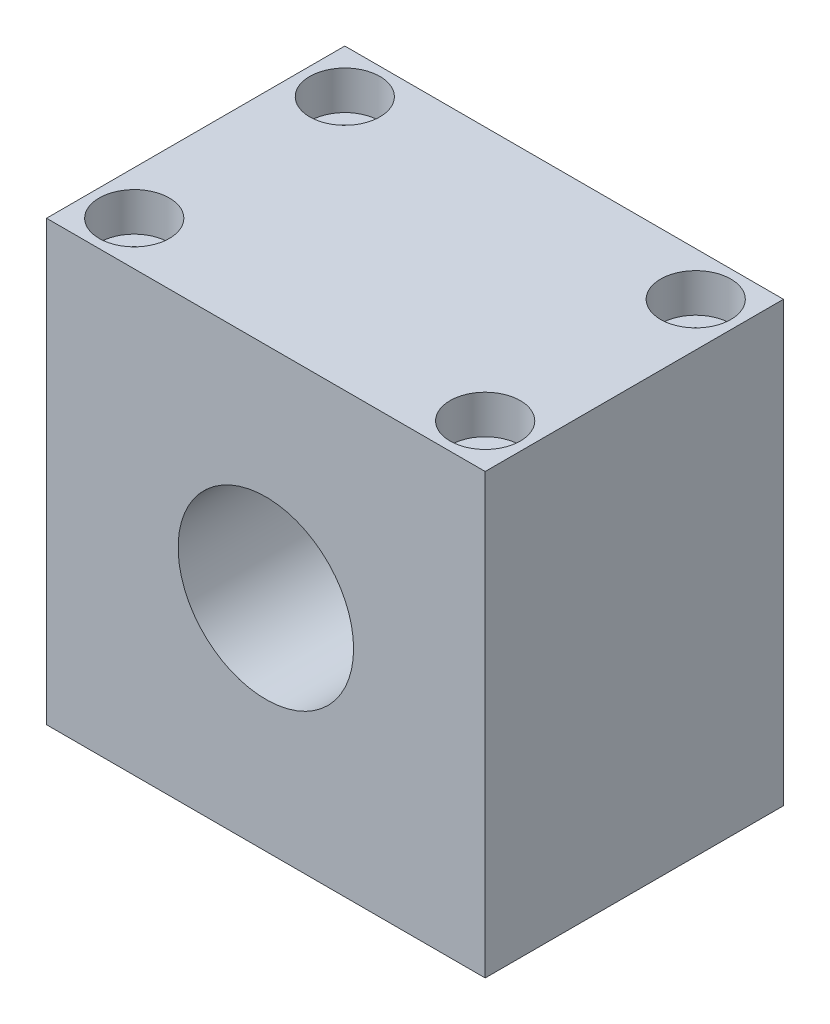
SolidWorks part; units mm, degrees
ref_plane "Front Plane" through (0, 0, 0) normal (0, 0, 1) x (1, 0, 0)
ref_plane "Top Plane" through (0, 0, 0) normal (0, 1, 0) x (1, 0, 0)
ref_plane "Right Plane" through (0, 0, 0) normal (1, 0, 0) x (0, 0, -1)
sketch "Sketch1" plane through (0, 0, 0) normal (0, 0, 1) x (1, 0, 0)
  line L1 (-25, -25) -> (25, -25)
  line L2 (-25, -25) -> (-25, 25)
  line L3 (-25, 25) -> (25, 25)
  line L4 (25, -25) -> (25, 25)
  line L5 (-25, -25) -> (25, 25) construction
  line L6 (-25, 25) -> (25, -25) construction
  point P0 (0, 0)
  dimension "D1" = 50
  dimension "D2" = 50
extrude "Boss-Extrude1" add sketch "Sketch1" along normal blind 34
sketch "Sketch2" plane through (0, 25, 0) normal (0, 1, 0) x (1, 0, 0)
  line L6 (25, -34) -> (-25, -34)
  line L8 (0, -17) -> (0, 9.8515) construction
  line L9 (0, -17) -> (31.6578, -17) construction
  line L10 (25, -34) -> (25, 0)
  line L11 (25, 0) -> (-25, 0)
  line L12 (-25, -34) -> (-25, 0)
  line L13 (25, -34) -> (-25, 0) construction
  line L14 (25, 0) -> (-25, -34) construction
  point P0 (0, -17)
  point P9 (-20, -5)
  point P13 (20, -5)
  point P16 (-20, -29)
  point P17 (20, -29)
  dimension "D1" = 5
  dimension "D2" = 5
  dimension "D3" = 34
  dimension "D4" = 50
hole_wizard "CBORE for M4 Hex Socket Head Cap Screw1" positions "Sketch3" profile "Sketch4" counterbore size "M4" standard "ISO" end condition through all
sketch "Sketch3" plane through (0, 25, 0) normal (0, 1, 0) x (1, 0, 0)
  point P0 (-20, -5)
  point P3 (20, -5)
  point P6 (20, -29)
  point P9 (-20, -29)
sketch "Sketch4" plane through (-20, 25, 5) normal (1, 0, 0) x (0, 0, 1)
  line L0 (0, 0) -> (0, 50)
  line L1 (0, 50) -> (2.25, 50)
  line L3 (2.25, 50) -> (2.25, 4.4)
  line L4 (2.25, 4.4) -> (4, 4.4)
  line L5 (4, 4.4) -> (4, 0)
  line L7 (4, 0) -> (0, 0)
  line L11 (0, -6.35) -> (0, 107.95) construction
  dimension "Thru Hole Dia." = 4.5
  dimension "Thru Hole Depth" = 50
  dimension "C'Bore Dia." = 8
  dimension "C'Bore Depth" = 4.4
sketch "Sketch6" plane through (0, 0, 34) normal (0, 0, 1) x (1, 0, 0)
  line L0 (-25, -25) -> (25, -25) construction
  line L1 (25, 25) -> (-25, 25) construction
  circle A0 centre (0, 0) radius 10
  dimension "D1" = 25
  dimension "D2" = 25
extrude "Cut-Extrude1" cut sketch "Sketch6" against normal through all
